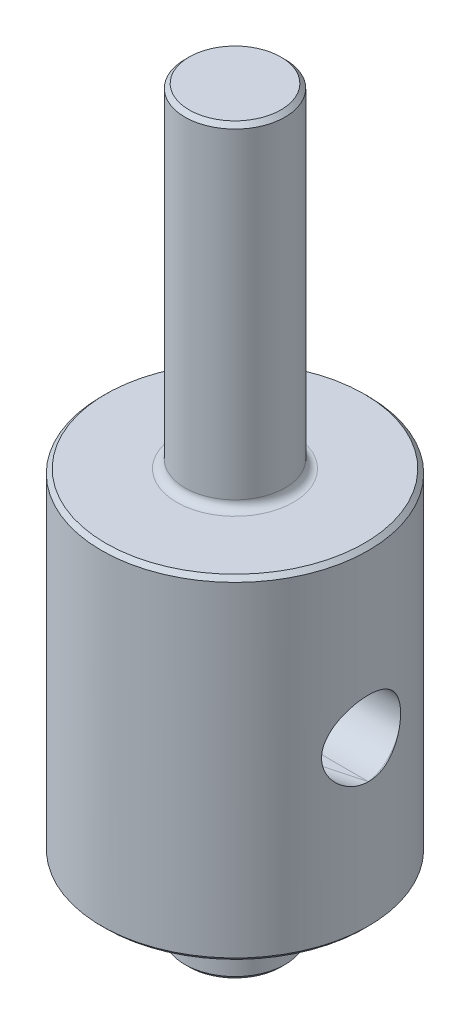
SolidWorks part; units mm, degrees
ref_plane "Plano frontal" through (0, 0, 0) normal (0, 0, 1) x (1, 0, 0)
ref_plane "Plano superior" through (0, 0, 0) normal (0, 1, 0) x (1, 0, 0)
ref_plane "Plano direito" through (0, 0, 0) normal (1, 0, 0) x (0, 0, -1)
sketch "Esboço1" plane through (0, 0, 0) normal (0, 0, 1) x (1, 0, 0)
  line L0 (0, 0) -> (0, 26.74) construction
  line L1 (0, 0) -> (8, 0) construction
  line L2 (0, 30) -> (3, 30)
  line L3 (3, 10) -> (3, 30)
  line L4 (8, 10) -> (3, 10)
  line L11 (8, 10) -> (8, -10)
  line L12 (0, 30) -> (0, 0)
  line L17 (3, -10) -> (8, -10)
  line L18 (3, -14.5) -> (3, -10)
  line L21 (3, -14.5) -> (0, -14.5)
  line L22 (0, -14.5) -> (0, 0)
  point P16 (8, 0)
  dimension "D1" = 6
  dimension "D2" = 6
  dimension "D5" = 16
  dimension "D6" = 20
  dimension "D7" = 20
  dimension "D9" = 4.5
revolve "Revolução1" add sketch "Esboço1" angle 360 about L0
ref_plane "Plano1" through (-8, 0, 0) normal (-1, 0, 0) x (0, 0, 1)
ref_plane "Plano2" through (8, 0, 0) normal (1, 0, 0) x (0, 0, -1)
sketch "Esboço2" plane through (-8, 0, 0) normal (-1, 0, 0) x (0, 0, 1)
  circle A0 centre (0, 0) radius 2.25
  dimension "D1" = 4.5
extrude "Corte-extrusão2" cut sketch "Esboço2" against normal through all
sketch "Esboço4" plane through (0, 0, 0) normal (0, 1, 0) x (1, 0, 0)
  line L0 (8, 0) -> (-8, 0)
  line L1 (0, 0) -> (-6.9282, -4) construction
  line L2 (8, 0) -> (-6.9282, -4)
  arc A0 (7.6771, -2.25) -> (7.6771, 2.25) centre (0, 0) ccw construction
  circle A1 centre (0, 0) radius 8 construction
  dimension "D1" = 30
ref_plane "Plano3" through (-6.9282, 0, 4) normal (-0.9659, 0, 0.2588) x (0.2588, 0, 0.9659)
sketch "Esboço7" plane through (-6.9282, 0, 4) normal (-0.9659, 0, 0.2588) x (0.2588, 0, 0.9659)
  circle A0 centre (0, 0) radius 2.25
  dimension "D1" = 4.5
extrude "Corte-extrusão6" cut sketch "Esboço7" against normal through all both and the other way through all
sketch "Sketch1" plane through (0, 0, 0) normal (0, 1, 0) x (1, 0, 0)
  line L0 (8, 0) -> (-10.8444, 0)
  line L1 (-10.8444, 0) -> (-10.4957, -4.9559)
  line L2 (-10.4957, -4.9559) -> (8, 0)
  line L3 (8, 0) -> (-6.9282, -4) construction
extrude "Cut-Extrude1" cut sketch "Sketch1" against normal mid plane 4.5
sketch "Sketch2" plane through (0, 0, 0) normal (0, 0, 1) x (1, 0, 0)
  line L0 (7.5, -10) -> (8, 10)
  line L1 (-8, -10) -> (8, -10) construction
  line L2 (8, -7.7) -> (8, 7.7) construction
  line L3 (8, 10) -> (-8, 10) construction
  line L4 (8, 10) -> (8, -10)
  line L5 (8, -10) -> (7.5, -10)
  dimension "D1" = 0.5
revolve "Cut-Revolve1" [suppressed] cut sketch "Sketch2" angle 360
fillet "Fillet1" radius 0.5 2 edges at (0, -10, -3) (0, 10, -3)
chamfer "Chamfer1" distance 0.25 angle 45 2 edges at (0, -14.5, -3) (0, 30, -3)
chamfer "Chamfer3" [suppressed] distance 0.25 angle 45
chamfer "Chamfer4" distance 0.25 angle 45 2 edges at (0, -10, -8) (0, 10, -8)
